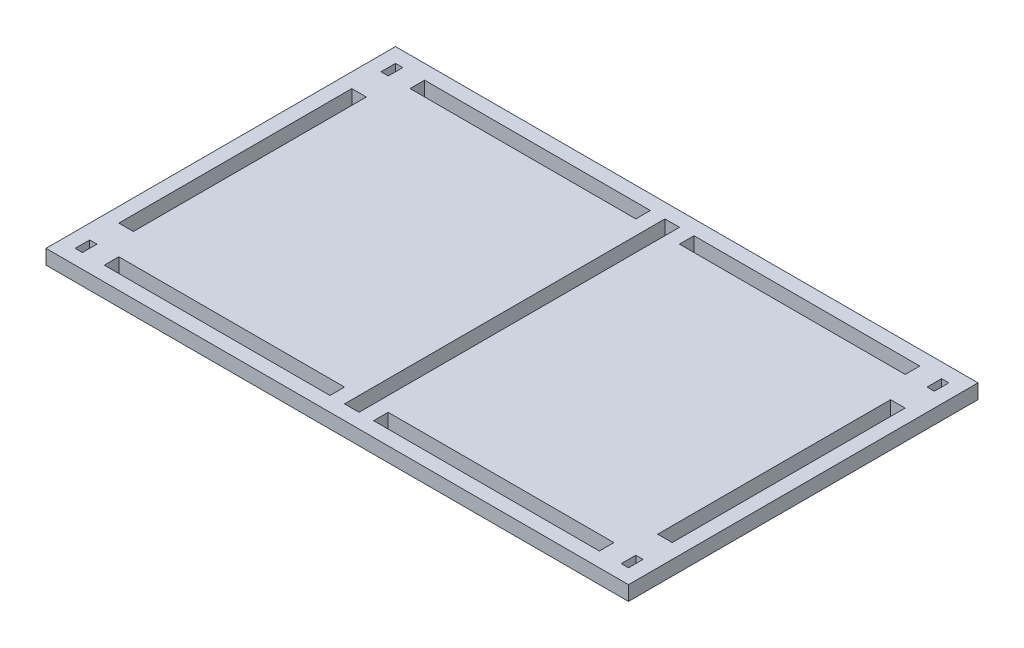
SolidWorks part; units mm, degrees
ref_plane "Front Plane" through (0, 0, 0) normal (0, 0, 1) x (1, 0, 0)
ref_plane "Top Plane" through (0, 0, 0) normal (0, 1, 0) x (1, 0, 0)
ref_plane "Right Plane" through (0, 0, 0) normal (1, 0, 0) x (0, 0, -1)
sketch "Sketch1" plane through (0, 0, 0) normal (0, 1, 0) x (1, 0, 0)
  line L0 (0, 76.2) -> (0, -76.2) construction
  line L1 (127, -76.2) -> (-127, -76.2)
  line L2 (127, -76.2) -> (127, 76.2)
  line L3 (127, 76.2) -> (-127, 76.2)
  line L4 (-127, -76.2) -> (-127, 76.2)
  line L5 (127, -76.2) -> (-127, 76.2) construction
  line L6 (127, 76.2) -> (-127, -76.2) construction
  line L11 (120.65, -50.8) -> (114.3, -50.8)
  line L12 (120.65, -50.8) -> (120.65, 50.8)
  line L13 (120.65, 50.8) -> (114.3, 50.8)
  line L14 (114.3, -50.8) -> (114.3, 50.8)
  line L15 (120.65, -50.8) -> (114.3, 50.8) construction
  line L16 (120.65, 50.8) -> (114.3, -50.8) construction
  line L17 (3.175, -69.85) -> (-3.175, -69.85)
  line L18 (3.175, -69.85) -> (3.175, 69.85)
  line L19 (3.175, 69.85) -> (-3.175, 69.85)
  line L20 (-3.175, -69.85) -> (-3.175, 69.85)
  line L21 (3.175, -69.85) -> (-3.175, 69.85) construction
  line L22 (3.175, 69.85) -> (-3.175, -69.85) construction
  line L23 (-120.65, -50.8) -> (-114.3, -50.8)
  line L24 (-114.3, -50.8) -> (-114.3, 50.8)
  line L25 (-120.65, -50.8) -> (-120.65, 50.8)
  line L26 (-120.65, 50.8) -> (-114.3, 50.8)
  line L27 (-127, 0) -> (127, 0) construction
  line L28 (-107.95, 69.85) -> (-9.525, 69.85)
  line L29 (-107.95, 69.85) -> (-107.95, 63.5051)
  line L30 (-107.95, 63.5051) -> (-9.525, 63.5051)
  line L31 (-9.525, 69.85) -> (-9.525, 63.5051)
  line L36 (9.525, -63.5102) -> (107.95, -63.5102)
  line L37 (9.525, -63.5102) -> (9.525, -69.8551)
  line L38 (9.525, -69.8551) -> (107.95, -69.8551)
  line L39 (107.95, -63.5102) -> (107.95, -69.8551)
  line L40 (9.525, 63.5051) -> (107.95, 63.5051)
  line L41 (9.525, 63.5051) -> (9.525, 69.85)
  line L42 (9.525, 69.85) -> (107.95, 69.85)
  line L43 (107.95, 63.5051) -> (107.95, 69.85)
  line L44 (-9.525, -69.85) -> (-9.525, -63.5051)
  line L45 (-107.95, -69.85) -> (-107.95, -63.5051)
  line L46 (-107.95, -69.85) -> (-9.525, -69.85)
  line L47 (-107.95, -63.5051) -> (-9.525, -63.5051)
  line L48 (-117.475, -63.5051) -> (-120.65, -63.5051)
  line L49 (117.475, -63.5051) -> (120.65, -63.5051)
  line L50 (117.475, -63.5051) -> (117.475, -69.85)
  line L51 (117.475, -69.85) -> (120.65, -69.85)
  line L52 (120.65, -63.5051) -> (120.65, -69.85)
  line L53 (-120.65, -63.5051) -> (-120.65, -69.85)
  line L54 (-117.475, -63.5051) -> (-117.475, -69.85)
  line L55 (-117.475, -69.85) -> (-120.65, -69.85)
  line L56 (-120.65, 63.5051) -> (-120.65, 69.85)
  line L57 (-117.475, 69.85) -> (-120.65, 69.85)
  line L58 (-117.475, 63.5051) -> (-117.475, 69.85)
  line L59 (-117.475, 63.5051) -> (-120.65, 63.5051)
  line L60 (117.475, 63.5051) -> (117.475, 69.85)
  line L61 (120.65, 63.5051) -> (120.65, 69.85)
  line L62 (117.475, 63.5051) -> (120.65, 63.5051)
  line L63 (117.475, 69.85) -> (120.65, 69.85)
  point P0 (0, 0)
  point P6 (117.475, 0)
  point P12 (0, 0)
  point P39 (107.95, -66.6826)
  point P45 (120.65, -66.6775)
  dimension "D1" = 254
  dimension "D2" = 152.4
  dimension "D3" = 25.4
  dimension "D4" = 25.4
  dimension "D5" = 6.35
  dimension "D6" = 6.35
  dimension "D7" = 6.35
  dimension "D8" = 6.35
  dimension "D9" = 6.35
  dimension "D10" = 6.35
  dimension "D11" = 6.3449
  dimension "D12" = 6.3449
  dimension "D13" = 3.175
  dimension "D14" = 6.3449
  dimension "D15" = 6.35
  dimension "D16" = 6.35
  dimension "D17" = 6.35
  dimension "D18" = 6.35
  dimension "D19" = 6.3449
  dimension "D20" = 6.35
  dimension "D21" = 6.35
  dimension "D43" = 6.3449
  dimension "D44" = 6.35
  dimension "D45" = 6.35
extrude "Boss-Extrude1" add sketch "Sketch1" along normal blind 6.35
